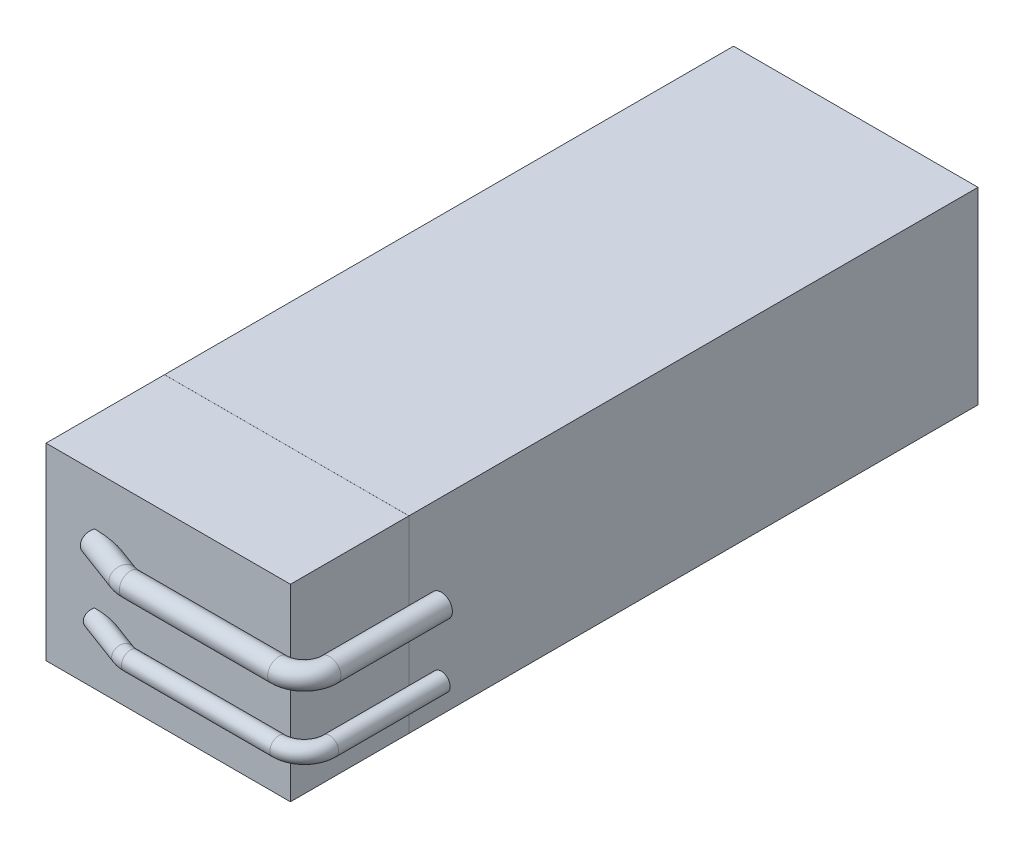
SolidWorks part; units mm, degrees
ref_plane "Plan de face" through (0, 0, 0) normal (0, 0, 1) x (1, 0, 0)
ref_plane "Plan de dessus" through (0, 0, 0) normal (0, 1, 0) x (1, 0, 0)
ref_plane "Plan de droite" through (0, 0, 0) normal (1, 0, 0) x (0, 0, -1)
sketch "Esquisse1" plane through (0, 0, 0) normal (1, 0, 0) x (0, 0, -1)
  line L1 (0, 0) -> (-135, 0)
  line L2 (0, 0) -> (0, 37)
  line L3 (0, 37) -> (-135, 37)
  line L4 (-135, 0) -> (-135, 37)
  dimension "D1" = 135
  dimension "D2" = 37
extrude "Boss.-Extru.1" add sketch "Esquisse1" along normal blind 48
ref_plane "Plan1" through (0, 12, 0) normal (0, -1, 0) x (-1, 0, 0)
ref_plane "Plan2" through (0, 25, 0) normal (0, -1, 0) x (-1, 0, 0)
sketch "Esquisse2" plane through (0, 12, 0) normal (0, -1, 0) x (-1, 0, 0)
  line L0 (-20.2021, -138.6272) -> (-49.3424, -138.6272)
  line L1 (-54.3424, -133.6272) -> (-54.3424, -111.7321)
  line L2 (-18.4574, -138.3129) -> (-9.5598, -135)
  line L3 (-48, -135) -> (0, -135) construction
  arc A0 (-54.3424, -133.6272) -> (-49.3424, -138.6272) centre (-49.3424, -133.6272) ccw
  arc A1 (-20.2021, -138.6272) -> (-18.4574, -138.3129) centre (-20.2021, -133.6272) ccw
  dimension "D1" = 5
  dimension "D2" = 5
ref_plane "Plan3" through (0, 0, 111.7321) normal (0, 0, -1) x (-1, 0, 0)
sketch "Esquisse3" plane through (0, 0, 111.7321) normal (0, 0, -1) x (-1, 0, 0)
  circle A0 centre (-54.3424, 12) radius 1.75
  circle A1 centre (-54.3424, 25) radius 2.1877
  dimension "D1" = 3.5
  dimension "D2" = 13
sweep "Balayage1" add profiles "Esquisse3" path "Esquisse2"
sketch "Esquisse4" plane through (0, 0, 111.7321) normal (0, 0, -1) x (-1, 0, 0)
  line L1 (0, 0) -> (-48, 0)
  line L2 (0, 0) -> (0, 37)
  line L3 (0, 37) -> (-48, 37)
  line L4 (-48, 0) -> (-48, 37)
extrude "Enlèv. mat.-Extru.1" cut sketch "Esquisse4" against normal blind 0.01
ref_plane "Plan4" through (24, 0, 0) normal (1, 0, 0) x (0, 0, -1)
